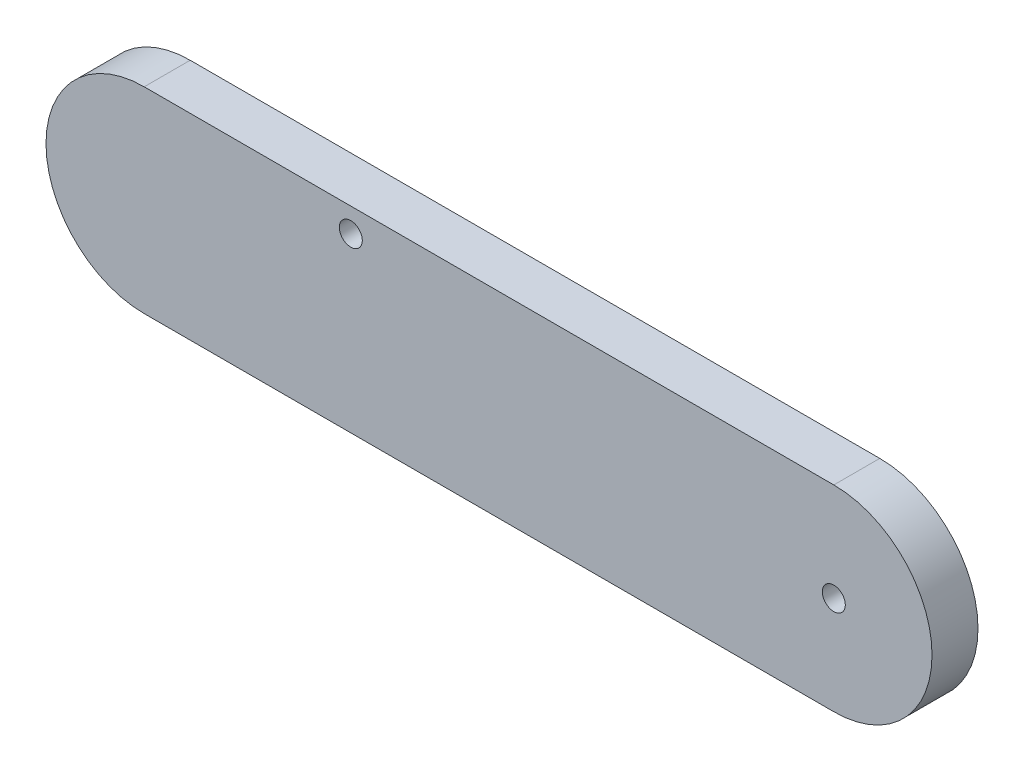
SolidWorks part; units mm, degrees
material "Mahogany"
ref_plane "Front Plane" through (0, 0, 0) normal (0, 0, 1) x (1, 0, 0)
ref_plane "Top Plane" through (0, 0, 0) normal (0, 1, 0) x (1, 0, 0)
ref_plane "Right Plane" through (0, 0, 0) normal (1, 0, 0) x (0, 0, -1)
sketch "Sketch1" plane through (0, 0, 0) normal (0, 0, 1) x (1, 0, 0)
  line L0 (-78.3383, 0) -> (71.6617, 0) construction
  line L1 (-78.3383, 21.365) -> (71.6617, 21.365)
  line L2 (-78.3383, -21.365) -> (71.6617, -21.365)
  arc A0 (-78.3383, 21.365) -> (-78.3383, -21.365) centre (-78.3383, 0) ccw
  arc A1 (71.6617, -21.365) -> (71.6617, 21.365) centre (71.6617, 0) ccw
  circle A3 centre (71.6617, 0) radius 2.5
  circle A4 centre (-33.4028, 16.125) radius 2.5
  point P3 (-3.3383, 0)
  dimension "D3" = 5
  dimension "D4" = 5
  dimension "D1" = 150
  dimension "D5" = 5.24
  dimension "D6" = 45.24
extrude "Boss-Extrude1" add sketch "Sketch1" along normal blind 10
